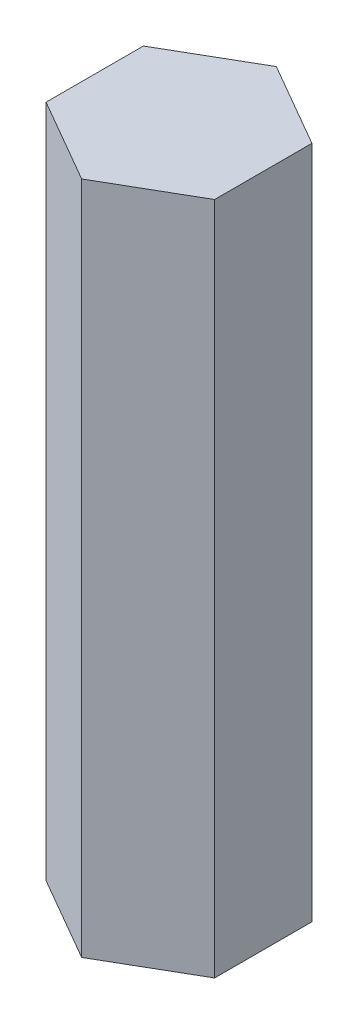
SolidWorks part; units mm, degrees
ref_plane "Front Plane" through (0, 0, 0) normal (0, 0, 1) x (1, 0, 0)
ref_plane "Top Plane" through (0, 0, 0) normal (0, 1, 0) x (1, 0, 0)
ref_plane "Right Plane" through (0, 0, 0) normal (1, 0, 0) x (0, 0, -1)
sketch "Sketch1" plane through (0, 0, 0) normal (0, 1, 0) x (1, 0, 0)
  line L1 (0, 7.3323) -> (-6.35, 3.6662)
  line L2 (-6.35, 3.6662) -> (-6.35, -3.6662)
  line L3 (-6.35, -3.6662) -> (0, -7.3323)
  line L4 (0, -7.3323) -> (6.35, -3.6662)
  line L5 (6.35, -3.6662) -> (6.35, 3.6662)
  line L6 (6.35, 3.6662) -> (0, 7.3323)
  circle A0 centre (0, 0) radius 6.35 construction
  dimension "D1" = 12.7
extrude "Boss-Extrude1" add sketch "Sketch1" along normal blind 50.8
